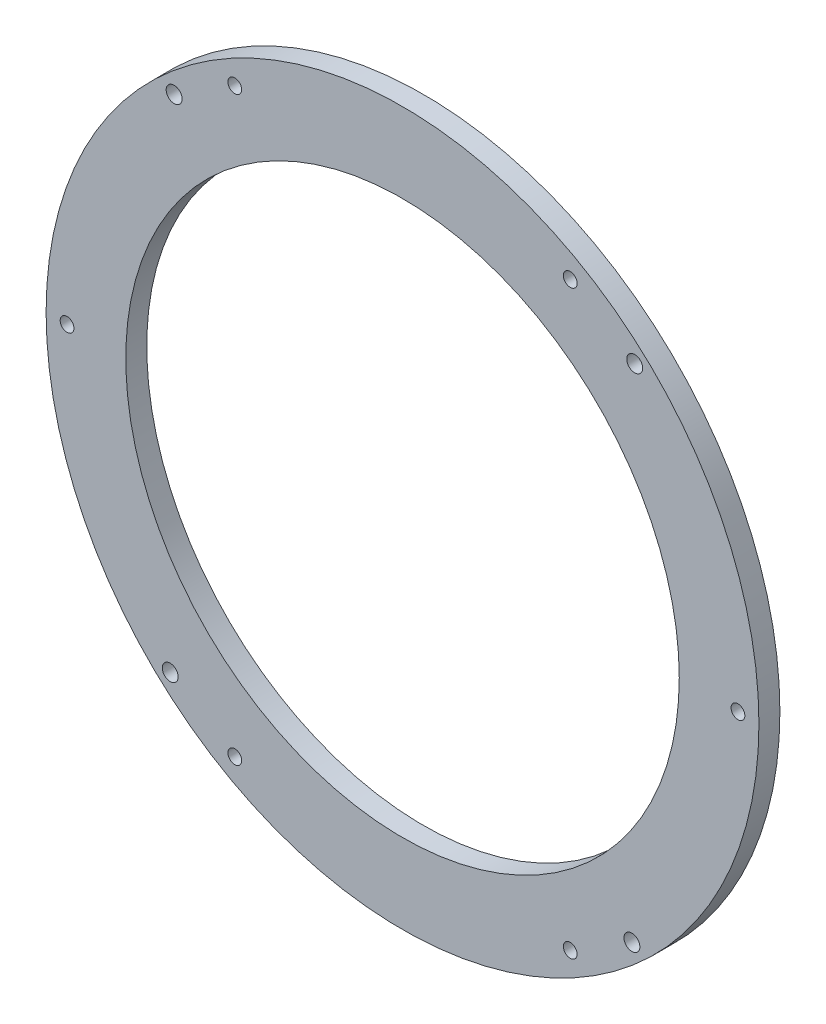
SolidWorks part; units mm, degrees
ref_plane "Front Plane" through (0, 0, 0) normal (0, 0, 1) x (1, 0, 0)
ref_plane "Top Plane" through (0, 0, 0) normal (0, 1, 0) x (1, 0, 0)
ref_plane "Right Plane" through (0, 0, 0) normal (1, 0, 0) x (0, 0, -1)
sketch "Sketch1" plane through (0, 0, 0) normal (0, 0, 1) x (1, 0, 0)
  circle A0 centre (51.7384, 55.5933) radius 107.95
  circle A1 centre (51.7384, 55.5933) radius 83.82
extrude "Boss-Extrude1" add sketch "Sketch1" along normal blind 6.35
sketch "Sketch2" plane through (0, 0, 0) normal (0, 0, -1) x (-1, 0, 0)
  line L0 (-51.7384, 55.5933) -> (-51.7384, -52.3567) construction
  line L1 (-9.8284, -16.9969) -> (2.2366, -37.8941) construction
  circle A0 centre (-51.7384, 55.5933) radius 107.95 construction
  circle A1 centre (-51.7384, 55.5933) radius 83.82 construction
  circle A2 centre (-51.7384, 55.5933) radius 83.82 construction
  circle A3 centre (-0.9384, -32.3949) radius 2.085
  circle A4 centre (-102.5384, -32.3949) radius 2.085
  circle A5 centre (-153.3384, 55.5933) radius 2.085
  circle A6 centre (-102.5384, 143.5815) radius 2.085
  circle A7 centre (-0.9384, 143.5815) radius 2.085
  circle A8 centre (49.8616, 55.5933) radius 2.085
  circle A11 centre (-121.2122, -20.9415) radius 2.413
  circle A12 centre (18.6154, -20.0661) radius 2.413
  point P25 (-51.7384, 55.5933)
  dimension "D2" = 4.17
  dimension "D1" = 30
  dimension "D4" = 6.35
  dimension "D3" = 6
extrude "Cut-Extrude1" cut sketch "Sketch2" against normal blind 21.336
sketch "Sketch5" plane through (0, 0, 6.35) normal (0, 0, 1) x (1, 0, 0)
  circle A2 centre (122.0634, 131.2529) radius 2.413
  circle A3 centre (-17.4307, 132.1262) radius 2.413
extrude "Cut-Extrude4" cut sketch "Sketch5" against normal blind 6.35
